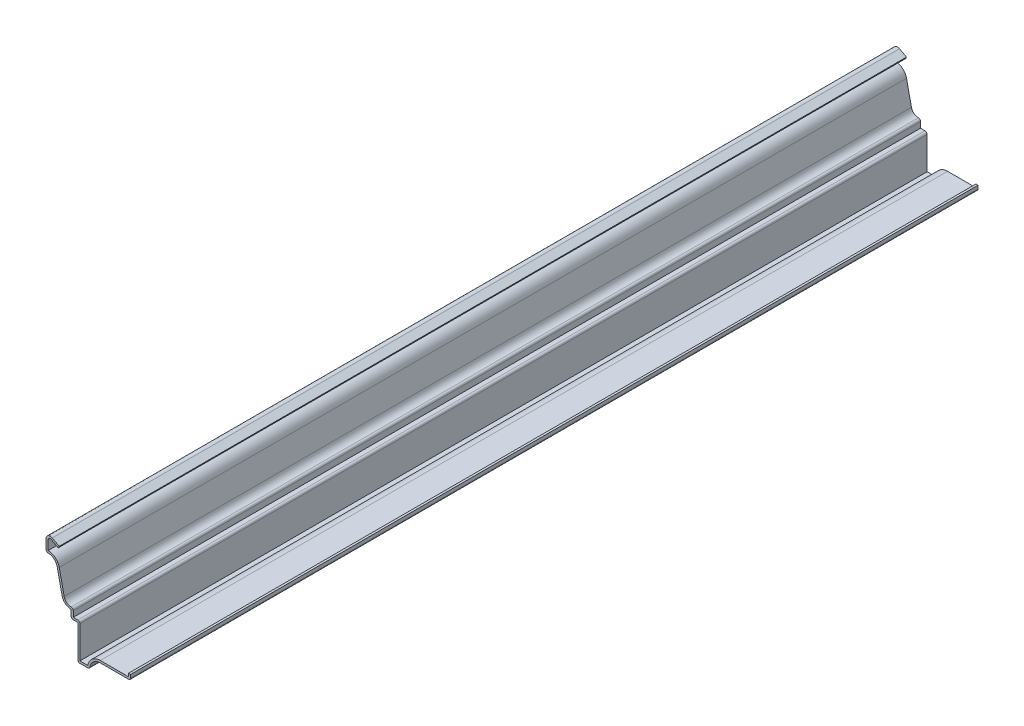
SolidWorks part; units mm, degrees
ref_plane "Front Plane" through (0, 0, 0) normal (0, 0, 1) x (1, 0, 0)
ref_plane "Top Plane" through (0, 0, 0) normal (0, 1, 0) x (1, 0, 0)
ref_plane "Right Plane" through (0, 0, 0) normal (1, 0, 0) x (0, 0, -1)
sketch "Sketch1" plane through (0, 0, 0) normal (0, 0, 1) x (1, 0, 0)
  line L0 (0, 57.15) -> (0, 0) construction
  line L1 (0, 0) -> (-31.75, 0) construction
  line L2 (0, 9.525) -> (0, 6.35)
  line L3 (0, 6.35) -> (-18.2562, 6.35)
  line L4 (-24.6062, 0) -> (-31.75, 0)
  line L5 (-31.75, 0) -> (-31.75, 20.6375)
  line L6 (-31.75, 20.6375) -> (-35.7188, 20.6375)
  line L7 (-35.7188, 20.6375) -> (-35.7188, 25.4)
  line L8 (-41.1489, 29.7792) -> (-44.0999, 43.3929)
  line L9 (-50.8, 47.625) -> (-50.8, 54.61)
  line L10 (-47.0647, 56.8512) -> (-42.8625, 54.61)
  line L11 (0, 57.15) -> (-58.199, 57.15) construction
  arc A0 (-18.2562, 6.35) -> (-24.6062, 0) centre (-18.2562, 0) ccw
  arc A1 (-35.7188, 25.4) -> (-41.1489, 29.7792) centre (-35.7188, 30.9562) cw
  arc A2 (-44.0999, 43.3929) -> (-50.8, 47.625) centre (-49.53, 42.2158) ccw
  arc A3 (-50.8, 54.61) -> (-47.0647, 56.8512) centre (-48.26, 54.61) cw
  point P20 (-51.8908, 53.3894)
  point P22 (-48.6442, 65.7122)
  point P23 (-50.8, 63.2183)
  point P24 (-43.2355, 53.3894)
  point P25 (-40.7399, 28.5771)
  point P26 (-45.2625, 56.6507)
  point P28 (0, 0)
  point P29 (0, 0)
  point P30 (-49.6918, 42.1804)
  point P31 (-46.7604, 57.15)
  point P32 (-42.8625, 54.61)
  dimension "D10" = 5.5562
  dimension "D16" = 2.54
  dimension "D1" = 24.6062
  dimension "D2" = 57.15
  dimension "D3" = 7.1437
  dimension "D4" = 3.9688
  dimension "D5" = 9.525
  dimension "D6" = 6.35
  dimension "D7" = 3.175
  dimension "D8" = 20.6375
  dimension "D9" = 4.7625
  dimension "D11" = 22.225
  dimension "D12" = 7.9375
  dimension "D13" = 42.8625
  dimension "D14" = 50.8
  dimension "D15" = 1.27
extrude "Extrude-Thin1" add sketch "Sketch1" against normal blind 508 thin
fillet "Fillet1" radius 1.27 7 edges at (0, 6.35, -254) (-24.6062, 0, -254) (-31.75, 0, -254) (-30.48, 21.9075, -254) (-35.7188, 20.6375, -254) (-34.4488, 26.8625, -254) (-50.8, 47.625, -254)
